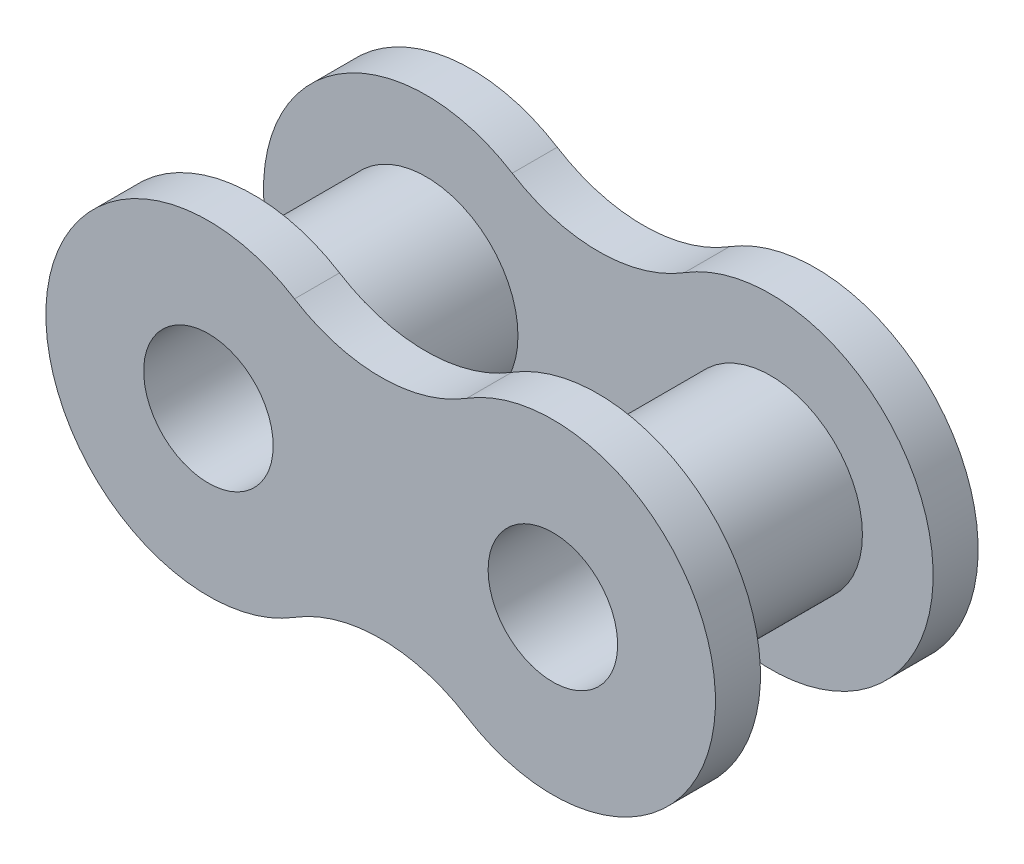
SolidWorks part; units mm, degrees
ref_plane "Front Plane" through (0, 0, 0) normal (0, 0, 1) x (1, 0, 0)
ref_plane "Top Plane" through (0, 0, 0) normal (0, 1, 0) x (1, 0, 0)
ref_plane "Right Plane" through (0, 0, 0) normal (1, 0, 0) x (0, 0, -1)
sketch "Sketch1" plane through (0, 0, 0) normal (0, 0, 1) x (1, 0, 0)
  line L0 (0, 0) -> (0, 3.945) construction
  circle A0 centre (-4.7625, 0) radius 1.7907
  circle A1 centre (-4.7625, 0) radius 2.54
  circle A2 centre (4.7625, 0) radius 2.54
  circle A3 centre (4.7625, 0) radius 1.7907
  dimension "D2" = 5.08
  dimension "D3" = 3.5814
  dimension "D1" = 4.7625
extrude "Boss-Extrude1" add sketch "Sketch1" along normal mid plane 4.7752
sketch "Sketch3" plane through (0, 0, 2.3876) normal (0, 0, 1) x (1, 0, 0)
  line L0 (0, 0) -> (0, 3.7043) construction
  line L1 (0, 0) -> (1.8804, 0) construction
  circle A0 centre (-4.7625, 0) radius 1.7907
  arc A1 (-2.3813, 3.8134) -> (-2.3813, -3.8134) centre (-4.7625, 0) ccw
  circle A2 centre (-4.7625, 0) radius 1.7907 construction
  circle A3 centre (4.7625, 0) radius 1.7907
  arc A4 (2.3813, 3.8134) -> (2.3813, -3.8134) centre (4.7625, 0) cw
  arc A6 (-2.3813, 3.8134) -> (2.3813, 3.8134) centre (0, 7.6268) ccw
  arc A7 (-2.3813, -3.8134) -> (2.3813, -3.8134) centre (0, -7.6268) cw
  dimension "D1" = 8.9916
  dimension "D2" = 4.4958
extrude "Boss-Extrude2" add sketch "Sketch3" along normal blind 1.2446
mirror "Mirror3" about plane through (0, 0, 0) normal (0, 0, 1) of "Boss-Extrude2"
